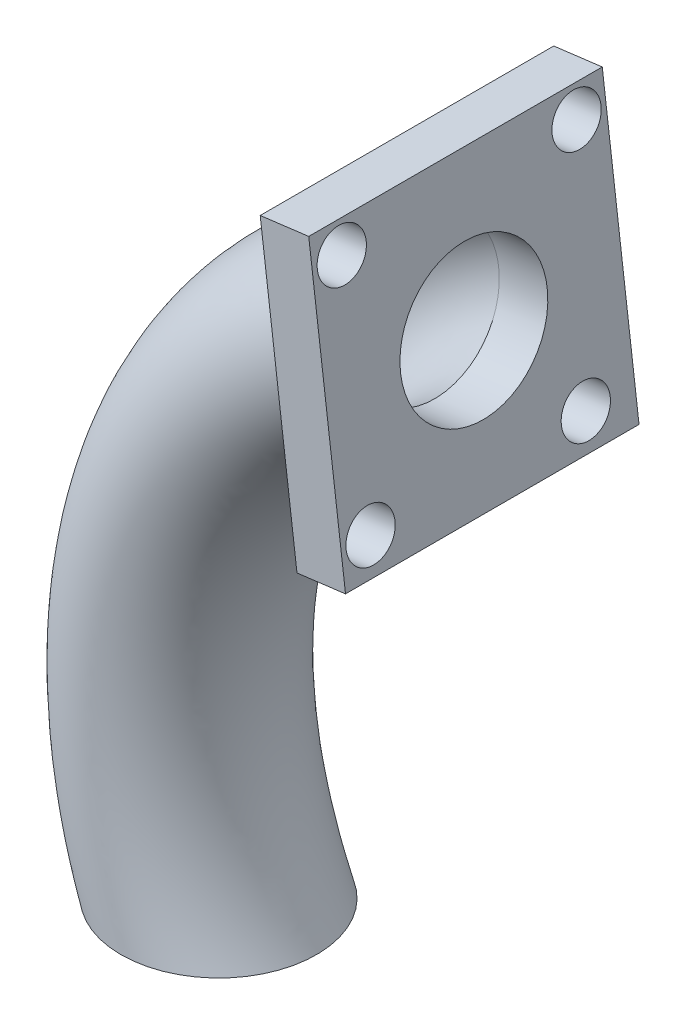
SolidWorks part; units mm, degrees
ref_plane "Front Plane" through (0, 0, 0) normal (0, 0, 1) x (1, 0, 0)
ref_plane "Top Plane" through (0, 0, 0) normal (0, 1, 0) x (1, 0, 0)
ref_plane "Right Plane" through (0, 0, 0) normal (1, 0, 0) x (0, 0, -1)
sketch "Sketch1" plane through (0, 0, 0) normal (0, 1, 0) x (1, 0, 0)
  circle A0 centre (0, 0) radius 7.5
  circle A1 centre (0, 0) radius 10
  dimension "D1" = 15
  dimension "D2" = 20
sketch "Sketch2" plane through (0, 0, 0) normal (0, 0, 1) x (1, 0, 0)
  arc A0 (0, 0) -> (21.1182, 62.669) centre (46.1008, 19.3576) cw
  point P3 (0, 0)
  dimension "D1" = 50
sweep "Sweep3" add profiles "Sketch1" path "Sketch2"
sketch "Sketch4" plane through (28.5786, 3.6101, 0) normal (0.9921, 0.1253, 0) x (0, 0, -1)
  line L0 (0, 59.5282) -> (0, 0) construction
  line L1 (-15, 74.5282) -> (15, 74.5282)
  line L2 (-15, 74.5282) -> (-15, 44.5282)
  line L3 (-15, 44.5282) -> (15, 44.5282)
  line L4 (15, 74.5282) -> (15, 44.5282)
  line L5 (-15, 74.5282) -> (15, 44.5282) construction
  line L6 (-15, 44.5282) -> (15, 74.5282) construction
  line L7 (10, 0) -> (10, 59.5282) construction
  circle A1 centre (-12, 71.5282) radius 2.5
  circle A2 centre (12, 71.5282) radius 2.5
  circle A3 centre (10, 48.0357) radius 2.5
  circle A4 centre (-12, 48.0357) radius 2.5
  circle A5 centre (0, 59.5282) radius 7.5
  point P0 (0, 59.5282)
  dimension "D3" = 5
  dimension "D1" = 30
  dimension "D2" = 30
  dimension "D4" = 3
extrude "Boss-Extrude3" add sketch "Sketch4" along normal blind 5
